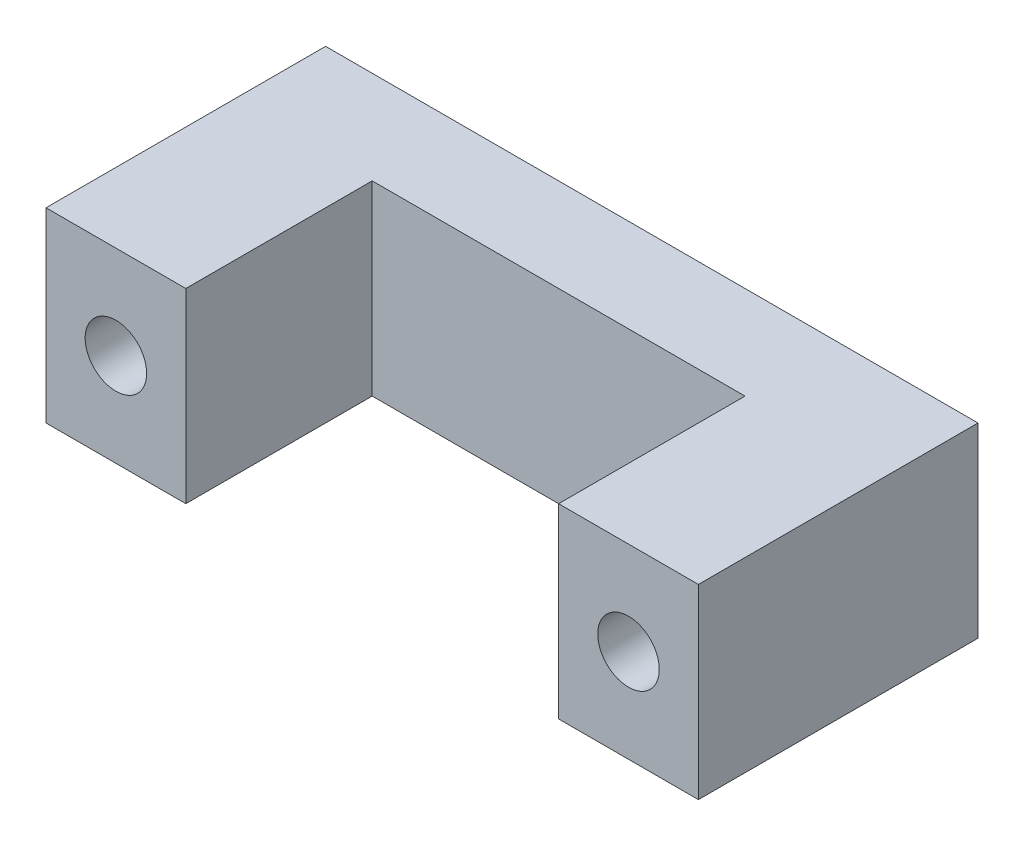
SolidWorks part; units mm, degrees
ref_plane "Front Plane" through (0, 0, 0) normal (0, 0, 1) x (1, 0, 0)
ref_plane "Top Plane" through (0, 0, 0) normal (0, 1, 0) x (1, 0, 0)
ref_plane "Right Plane" through (0, 0, 0) normal (1, 0, 0) x (0, 0, -1)
sketch "Sketch1" plane through (0, 0, 0) normal (0, 0, 1) x (1, 0, 0)
  line L0 (0, 5) -> (0, -5) construction
  line L1 (17.5, -5) -> (-17.5, -5)
  line L2 (17.5, -5) -> (17.5, 5)
  line L3 (17.5, 5) -> (-17.5, 5)
  line L4 (-17.5, -5) -> (-17.5, 5)
  line L5 (17.5, -5) -> (-17.5, 5) construction
  line L6 (17.5, 5) -> (-17.5, -5) construction
  circle A0 centre (-13.75, 0) radius 1.65
  circle A1 centre (13.75, 0) radius 1.65
  point P0 (0, 0)
  dimension "D4" = 3.3
  dimension "D1" = 13.75
  dimension "D2" = 10
  dimension "D3" = 35
extrude "Boss-Extrude1" add sketch "Sketch1" along normal blind 15
sketch "Sketch2" plane through (0, 0, 15) normal (0, 0, 1) x (1, 0, 0)
  line L0 (17.5, 5) -> (-17.5, 5) construction
  line L1 (10, -5) -> (-10, -5)
  line L2 (10, -5) -> (10, 5)
  line L3 (10, 5) -> (-10, 5)
  line L4 (-10, -5) -> (-10, 5)
  line L5 (10, -5) -> (-10, 5) construction
  line L6 (10, 5) -> (-10, -5) construction
  point P0 (0, 0)
  dimension "D1" = 20
extrude "Cut-Extrude1" cut sketch "Sketch2" against normal blind 10
